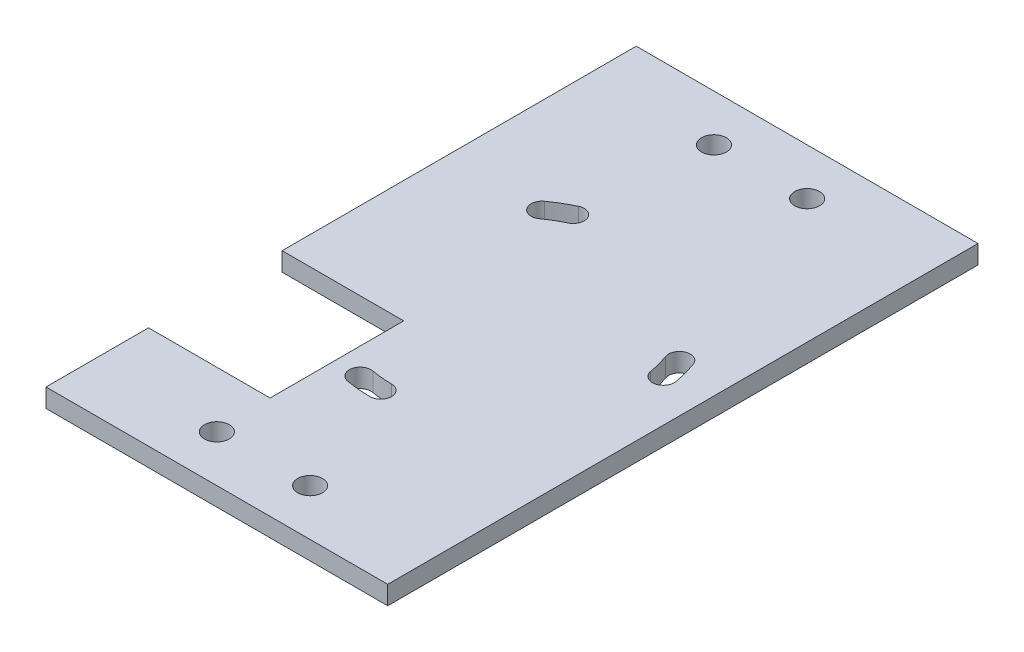
SolidWorks part; units mm, degrees
ref_plane "Ebene vorne" through (0, 0, 0) normal (0, 0, 1) x (1, 0, 0)
ref_plane "Ebene oben" through (0, 0, 0) normal (0, 1, 0) x (1, 0, 0)
ref_plane "Ebene rechts" through (0, 0, 0) normal (1, 0, 0) x (0, 0, -1)
sketch "OutlineRight" plane through (0, 0, 0) normal (1, 0, 0) x (0, 0, -1)
  line L1 (-95, 169.5) -> (-285, 169.5)
  line L2 (-95, 169.5) -> (-95, 163.5)
  line L3 (-95, 163.5) -> (-285, 163.5)
  line L4 (-285, 169.5) -> (-285, 163.5)
  line L5 (-190, 169.5) -> (-190, 212) construction
  line L6 (0, 218) -> (0, 227) construction
  line L8 (-190, 212) -> (-190, 217) construction
  line L9 (-190, 217) -> (-190, 227) construction
  point P4 (-190, 163.5)
sketch "Holes" plane through (0, 0, 0) normal (0, 1, 0) x (1, 0, 0)
  line L1 (0, -190) -> (-21.4267, -153.8216) construction
  line L2 (-24.4983, -155.8267) -> (0, -190) construction
  line L3 (0, -190) -> (-18.192, -152.0918) construction
  line L4 (40.6146, -179.1173) -> (0, -190) construction
  line L5 (41.4086, -182.6986) -> (0, -190) construction
  line L6 (0, -190) -> (39.5116, -175.619) construction
  line L7 (-7.4968, -231.3736) -> (0, -190) construction
  line L8 (0, -190) -> (-0.1984, -232.0469) construction
  line L9 (-3.8623, -231.8696) -> (0, -190) construction
  line L10 (0, -190) -> (-48.3248, -190) construction
  circle A8 centre (0, -190) radius 42.0474
  arc A9 (-24.4983, -155.8267) -> (-18.192, -152.0918) centre (0, -190) cw construction
  arc A10 (-19.7063, -148.9363) -> (-26.5375, -152.9821) centre (0, -190) ccw
  arc A11 (-16.6777, -155.2472) -> (-22.4591, -158.6713) centre (0, -190) ccw
  arc A12 (-16.6777, -155.2472) -> (-19.7063, -148.9363) centre (-18.192, -152.0918) ccw
  arc A13 (-26.5375, -152.9821) -> (-22.4591, -158.6713) centre (-24.4983, -155.8267) ccw
  arc A14 (39.5116, -175.619) -> (41.4086, -182.6986) centre (0, -190) cw construction
  arc A15 (44.8554, -182.0908) -> (42.8005, -174.4219) centre (0, -190) ccw
  arc A16 (37.9617, -183.3063) -> (36.2227, -176.816) centre (0, -190) ccw
  arc A17 (37.9617, -183.3063) -> (44.8554, -182.0908) centre (41.4086, -182.6986) ccw
  arc A18 (42.8005, -174.4219) -> (36.2227, -176.816) centre (39.5116, -175.619) ccw
  arc A19 (-0.1984, -232.0469) -> (-7.4968, -231.3736) centre (0, -190) cw construction
  arc A20 (-8.1208, -234.8176) -> (-0.215, -235.5469) centre (0, -190) ccw
  arc A21 (-6.8728, -227.9297) -> (-0.1819, -228.5469) centre (0, -190) ccw
  arc A22 (-6.8728, -227.9297) -> (-8.1208, -234.8176) centre (-7.4968, -231.3736) ccw
  arc A23 (-0.215, -235.5469) -> (-0.1819, -228.5469) centre (-0.1984, -232.0469) ccw
  point P6 (39.5116, -175.619)
  point P8 (-7.4968, -231.3736)
  point P11 (-24.4983, -155.8267)
  point P14 (-18.192, -152.0918)
  point P17 (-21.4267, -153.8216)
  point P23 (0, -190)
  point P24 (41.4086, -182.6986)
  point P27 (40.6146, -179.1173)
  point P33 (-3.8623, -231.8696)
  point P34 (-0.1984, -232.0469)
  point P38 (-3.8623, -231.8696)
sketch "Skizze3" plane through (0, 0, 0) normal (1, 0, 0) x (0, 0, -1)
  line L1 (-285, 169.5) -> (-95, 169.5)
  line L2 (-285, 169.5) -> (-285, 163.5)
  line L3 (-285, 163.5) -> (-95, 163.5)
  line L4 (-95, 169.5) -> (-95, 163.5)
sketch "OutlineTop" plane through (0, 0, 0) normal (0, 1, 0) x (1, 0, 0)
  line L0 (0, -95) -> (0, -285) construction
  line L1 (55, -285) -> (55, -95)
  line L2 (55, -285) -> (-55, -285)
  line L3 (-55, -285) -> (-55, -95)
  line L4 (55, -95) -> (-55, -95)
  line L5 (55, -285) -> (-55, -95) construction
  line L6 (-55, -285) -> (55, -95) construction
  line L16 (0, -190) -> (0, -150.9424) construction
  line L27 (-30, -285) -> (-30, -255)
  line L28 (-30, -285) -> (30, -285)
  line L29 (30, -285) -> (30, -255)
  line L30 (-30, -255) -> (30, -255)
  line L31 (0, -255) -> (-30, -255)
  line L32 (30, -255) -> (-30, -255)
  line L34 (30, -285) -> (-30, -285)
  line L35 (0, -190) -> (89.9295, -190) construction
  line L36 (30, -95) -> (-30, -95)
  line L39 (0, -125) -> (-30, -125)
  line L40 (-30, -125) -> (30, -125)
  line L41 (30, -95) -> (30, -125)
  line L42 (-30, -95) -> (30, -95)
  line L43 (-30, -95) -> (-30, -125)
  circle A0 centre (-15, -270) radius 3
  circle A1 centre (15, -270) radius 3
  circle A4 centre (15, -270) radius 3
  circle A5 centre (-15, -270) radius 3
  circle A6 centre (-15, -110) radius 3
  circle A7 centre (15, -110) radius 3
  circle A8 centre (15, -110) radius 3
  circle A9 centre (-15, -110) radius 3
  point P33 (0, -190)
extrude "Aufsatz-Linear austragen2" add sketch "Skizze3" along normal up to vertex (55 mm away) and the other way up to vertex (55 mm away) up to point (55, 0, 95)
sketch "Skizze8" plane through (0, 0, 0) normal (0, 1, 0) x (1, 0, 0)
  line L5 (-55, -252) -> (-55, -209)
  line L7 (-55, -209) -> (-15.8623, -209)
  line L8 (-15.8623, -209) -> (-15.8623, -252)
  line L9 (-15.8623, -252) -> (-55, -252)
extrude "Schnitt-Linear austragen5" cut sketch "Holes" along normal up to surface (169.5 mm away) up to face at (0, 169.5, 190)
extrude "Schnitt-Linear austragen6" cut sketch "OutlineTop" along normal up to surface (169.5 mm away) up to face at (-21.3082, 169.5, 154.0216)
extrude "Schnitt-Linear austragen7" cut sketch "Skizze8" along normal up to surface (169.5 mm away)
sketch "Skizze9" plane through (0, 0, 0) normal (0, 1, 0) x (1, 0, 0)
  circle A0 centre (-15, -110) radius 4
  circle A1 centre (15, -110) radius 4
  circle A2 centre (15, -270) radius 4
  circle A3 centre (-15, -270) radius 4
extrude "Schnitt-Linear austragen8" cut sketch "Skizze9" along normal up to surface (169.5 mm away) up to face at (15, 169.5, 267)
sketch "Skizze10" plane through (0, 169.5, 0) normal (0, 1, 0) x (1, 0, 0)
  line L0 (-55, -285) -> (-55, -95) construction
  line L1 (55, -95) -> (-55, -95) construction
  line L2 (-55, -209) -> (-15.8623, -209) construction
  line L4 (-15.8623, -209) -> (-15.8623, -252) construction
  point P0 (0, -190)
  dimension "D1" = 55
  dimension "D2" = 95
  dimension "D3" = 19
  dimension "D4" = 15.8623
